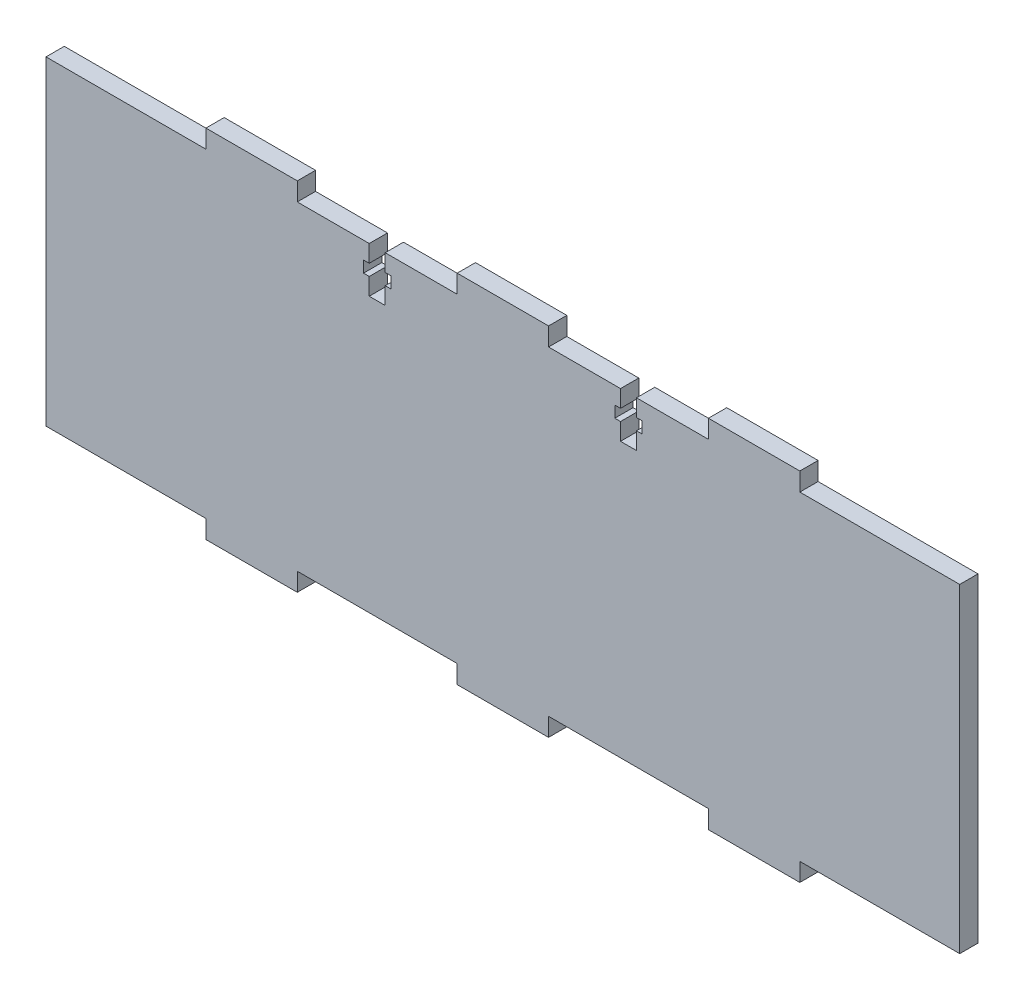
SolidWorks part; units mm, degrees
ref_plane "Front Plane" through (0, 0, 0) normal (0, 0, 1) x (1, 0, 0)
ref_plane "Top Plane" through (0, 0, 0) normal (0, 1, 0) x (1, 0, 0)
ref_plane "Right Plane" through (0, 0, 0) normal (1, 0, 0) x (0, 0, -1)
sketch "Sketch1" plane through (0, 0, 0) normal (0, 0, 1) x (1, 0, 0)
  line L1 (0, 0) -> (-200, 0)
  line L2 (0, 0) -> (0, 78)
  line L3 (0, 78) -> (-200, 78)
  line L4 (-200, 0) -> (-200, 78)
  dimension "D1" = 200
  dimension "D2" = 78
extrude "Boss-Extrude1" add sketch "Sketch1" along normal blind 4
sketch "Sketch2" plane through (0, 0, 4) normal (0, 0, 1) x (1, 0, 0)
  line L0 (-200, 74) -> (-200, 78)
  line L1 (-200, 78) -> (-200, 0) construction
  line L2 (-165, 74) -> (-145, 74)
  line L3 (0, 0) -> (0, 78) construction
  line L4 (0, 74) -> (0, 78)
  line L5 (0, 78) -> (-200, 78)
  line L6 (-165, 74) -> (-145, 74)
  line L7 (-110, 74) -> (-90, 74)
  line L8 (-55, 74) -> (-35, 74)
  line L9 (-110, 74) -> (-90, 74)
  line L10 (-55, 74) -> (-35, 74)
  line L11 (-200, 74) -> (-165, 74)
  line L12 (-145, 74) -> (-110, 74)
  line L13 (-90, 74) -> (-55, 74)
  line L14 (-35, 74) -> (0, 74)
  line L15 (-165, 74) -> (-165, 78)
  line L16 (-145, 74) -> (-145, 78)
  line L17 (-110, 74) -> (-110, 78)
  line L18 (-90, 74) -> (-90, 78)
  line L19 (-55, 74) -> (-55, 78)
  line L20 (-35, 74) -> (-35, 78)
  line L21 (-200, 39) -> (0, 39) construction
  line L22 (-35, 4) -> (-35, 0)
  line L23 (-55, 4) -> (-55, 0)
  line L24 (-90, 4) -> (-90, 0)
  line L25 (-110, 4) -> (-110, 0)
  line L26 (-145, 4) -> (-145, 0)
  line L27 (-165, 4) -> (-165, 0)
  line L28 (-35, 4) -> (0, 4)
  line L29 (-90, 4) -> (-55, 4)
  line L30 (-145, 4) -> (-110, 4)
  line L31 (-200, 4) -> (-165, 4)
  line L32 (-55, 4) -> (-35, 4)
  line L33 (-110, 4) -> (-90, 4)
  line L34 (-55, 4) -> (-35, 4)
  line L35 (-110, 4) -> (-90, 4)
  line L36 (-165, 4) -> (-145, 4)
  line L37 (0, 0) -> (-200, 0)
  line L38 (0, 4) -> (0, 0)
  line L39 (-165, 4) -> (-145, 4)
  line L40 (-200, 4) -> (-200, 0)
  line M9 (0, 0) -> (0, 78)
  line M10 (0, 78) -> (-200, 78)
  line M11 (-200, 78) -> (-200, 0)
  line M12 (-200, 0) -> (0, 0)
  dimension "D1" = 20
  dimension "D2" = 20
  dimension "D3" = 20
extrude "Cut-Extrude1" cut sketch "Sketch2" against normal up to surface (4 mm away) contours L11 L15 L5 M11 | L12 L17 L5 L16 | L13 L19 L5 L18 | L20 L14 M9 M10 | L31 L27 M11 M12 | L30 L26 L25 M12 | L29 L24 L23 M12 | L28 L22 M12 M9 up to face at (-100, 39, 0)
sketch "Sketch4" plane through (0, 74, 0) normal (0, 1, 0) x (1, 0, 0)
  line L0 (-145, -2) -> (-110, -2)
  line L1 (-145, 0) -> (-145, -4) construction
  line L2 (-110, 0) -> (-110, -4) construction
  line L3 (-110, 0) -> (-145, 0) construction
  line L4 (-129.25, -4) -> (-125.75, -4)
  line L5 (-129.25, -4) -> (-129.25, 0)
  line L6 (-129.25, 0) -> (-125.75, 0)
  line L7 (-125.75, -4) -> (-125.75, 0)
  line L8 (-129.25, -4) -> (-125.75, 0) construction
  line L9 (-129.25, 0) -> (-125.75, -4) construction
  line L10 (-100, 0) -> (-100, -4) construction
  line L11 (-90, 0) -> (-110, 0) construction
  line L12 (-90, -4) -> (-110, -4) construction
  line L13 (-70.75, 0) -> (-74.25, -4) construction
  line L14 (-70.75, -4) -> (-74.25, 0) construction
  line L15 (-74.25, -4) -> (-74.25, 0)
  line L16 (-70.75, 0) -> (-74.25, 0)
  line L17 (-70.75, -4) -> (-70.75, 0)
  line L18 (-70.75, -4) -> (-74.25, -4)
  point P6 (-127.5, -2)
  point P23 (-72.5, -2)
  line M2 (-110, 0) -> (-145, 0)
  line M4 (-145, -4) -> (-110, -4)
  dimension "D1" = 3.5
extrude "Cut-Extrude4" cut sketch "Sketch4" against normal blind 10 contours L7 L0 L5 M4 | L0 L7 L5 M2 | L18 L17 L16 L15
sketch "Sketch5" plane through (0, 0, 0) normal (0, 0, -1) x (-1, 0, 0)
  line L0 (127.5, 64) -> (127.5, 74) construction
  line L1 (125.75, 64) -> (129.25, 64) construction
  line L2 (100, 78) -> (100, 0) construction
  line L3 (130.5, 67.75) -> (124.5, 67.75)
  line L4 (130.5, 67.75) -> (130.5, 70.25)
  line L5 (130.5, 70.25) -> (124.5, 70.25)
  line L6 (124.5, 67.75) -> (124.5, 70.25)
  line L7 (130.5, 67.75) -> (124.5, 70.25) construction
  line L8 (130.5, 70.25) -> (124.5, 67.75) construction
  line L9 (90, 78) -> (110, 78) construction
  line L10 (110, 0) -> (90, 0) construction
  line L11 (69.5, 70.25) -> (75.5, 67.75) construction
  line L12 (69.5, 67.75) -> (75.5, 70.25) construction
  line L13 (72.5, 64) -> (72.5, 74) construction
  line L14 (75.5, 67.75) -> (75.5, 70.25)
  line L15 (69.5, 70.25) -> (75.5, 70.25)
  line L16 (69.5, 67.75) -> (69.5, 70.25)
  line L17 (69.5, 67.75) -> (75.5, 67.75)
  point P4 (127.5, 69)
  point P21 (72.5, 69)
  dimension "D1" = 10
  dimension "D2" = 6
  dimension "D3" = 2.5
extrude "Cut-Extrude5" cut sketch "Sketch5" against normal up to surface (4 mm away) up to face at (-100, 45.6667, 4)
